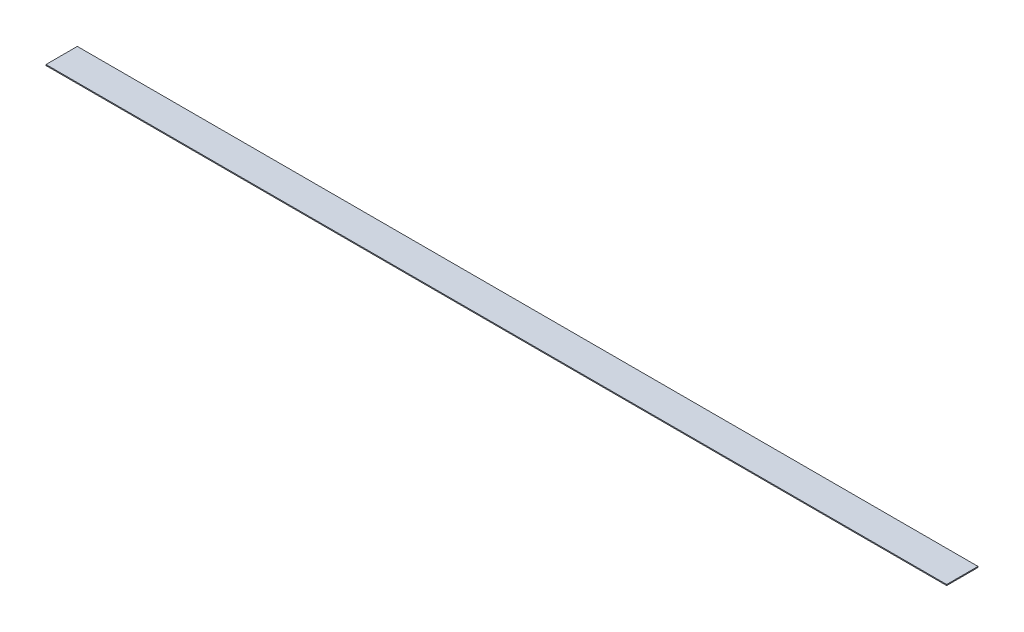
SolidWorks part; units mm, degrees
ref_plane "Front Plane" through (0, 0, 0) normal (0, 0, 1) x (1, 0, 0)
ref_plane "Top Plane" through (0, 0, 0) normal (0, 1, 0) x (1, 0, 0)
ref_plane "Right Plane" through (0, 0, 0) normal (1, 0, 0) x (0, 0, -1)
sketch "Sketch1" plane through (0, 0, 0) normal (0, 1, 0) x (1, 0, 0)
  line L1 (0, 0) -> (1460.5, 0)
  line L2 (0, 0) -> (0, 50.8)
  line L3 (0, 50.8) -> (1460.5, 50.8)
  line L4 (1460.5, 0) -> (1460.5, 50.8)
  dimension "D1" = 50.8
  dimension "D2" = 1460.5
extrude "Boss-Extrude1" add sketch "Sketch1" along normal blind 1.5875
